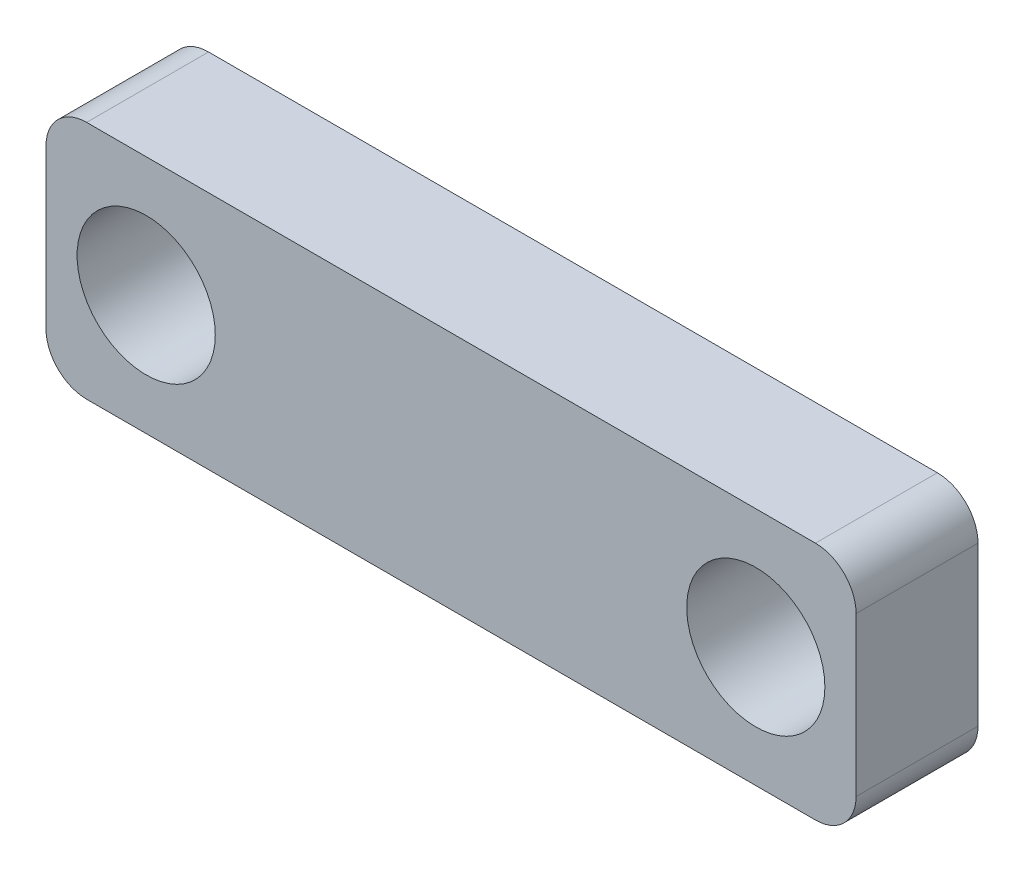
SolidWorks part; units mm, degrees
ref_plane "Plano frontal" through (0, 0, 0) normal (0, 0, 1) x (1, 0, 0)
ref_plane "Plano superior" through (0, 0, 0) normal (0, 1, 0) x (1, 0, 0)
ref_plane "Plano direito" through (0, 0, 0) normal (1, 0, 0) x (0, 0, -1)
ref_plane "Plane1" through (0, 0, 133.3657) normal (0, 0, 1) x (1, 0, 0)
sketch "Sketch2" plane through (0, 0, 133.3657) normal (0, 0, 1) x (1, 0, 0)
  line L1 (-31.2221, 40.9398) -> (-11.2895, 40.9398)
  line L2 (-31.2221, 40.9398) -> (-31.2221, 35.0398)
  line L3 (-31.2221, 35.0398) -> (-11.2895, 35.0398)
  line L4 (-11.2895, 40.9398) -> (-11.2895, 35.0398)
  dimension "D1" = 5.9
extrude "Boss-Extrude1" add sketch "Sketch2" along normal blind 3
fillet "Fillet1" radius 1 4 edges at (-11.2895, 35.0398, 134.8657) (-11.2895, 40.9398, 134.8657) (-31.2221, 35.0398, 134.8657) (-31.2221, 40.9398, 134.8657)
hole_wizard "M3 Clearance Hole1" positions "Sketch5" profile "Sketch3" hole size "M3" standard "ISO"
sketch "Sketch5" plane through (0, 0, 136.3657) normal (0, 0, 1) x (1, 0, 0)
  line L0 (-12.2895, 40.9398) -> (-30.2221, 40.9398) construction
  line L1 (-31.2221, 39.9398) -> (-31.2221, 36.0398) construction
  point P0 (-28.7571, 37.9898)
  point P2 (-13.7571, 37.9898)
  dimension "D1" = 2.95
  dimension "D2" = 2.95
  dimension "D3" = 15
  dimension "D4" = 2.465
sketch "Sketch3" plane through (-28.7571, 37.9898, 136.3657) normal (1, 0, 0) x (0, -1, 0)
  line L0 (0, 0) -> (0, 17.5215)
  line L1 (0, 17.5215) -> (1.7, 16.5)
  line L2 (1.7, 16.5) -> (1.7, 0)
  line L5 (1.7, 0) -> (0, 0)
  line L10 (0, 17.5215) -> (-1.7, 16.5) construction
  line L11 (0, -6.35) -> (0, 107.95) construction
  dimension "Hole Dia." = 3.4
  dimension "Hole Depth" = 16.5
  dimension "Drill Angle" = 118
